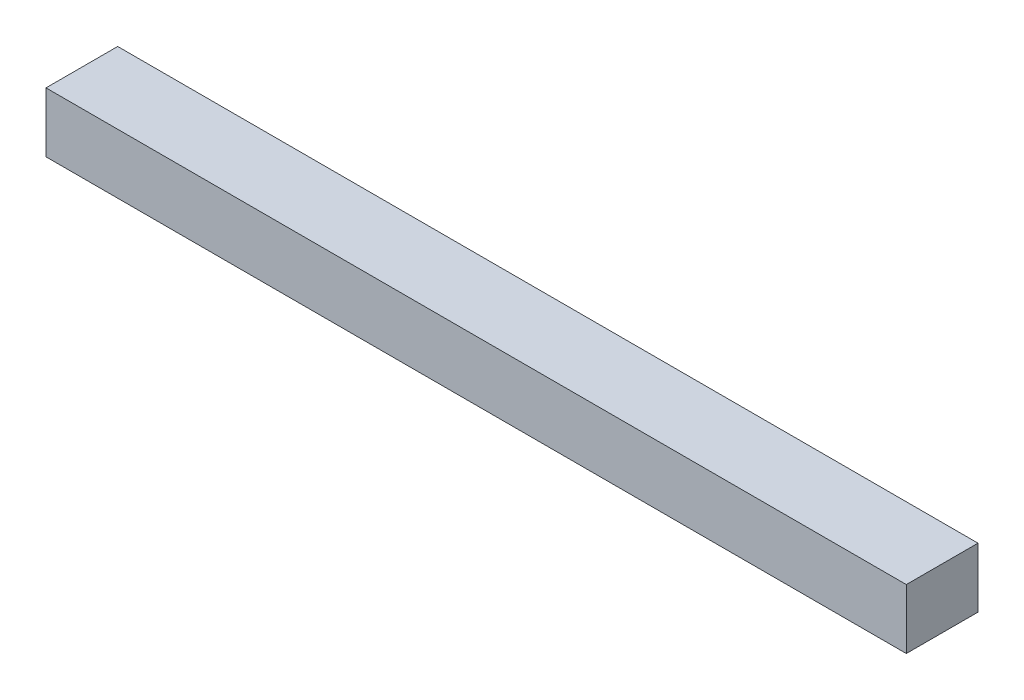
SolidWorks part; units mm, degrees
ref_plane "Спереди" through (0, 0, 0) normal (0, 0, 1) x (1, 0, 0)
ref_plane "Сверху" through (0, 0, 0) normal (0, 1, 0) x (1, 0, 0)
ref_plane "Справа" through (0, 0, 0) normal (1, 0, 0) x (0, 0, -1)
sketch "Эскиз2" plane through (0, 0, 0) normal (1, 0, 0) x (0, 0, -1)
  line L1 (-15, -12.5) -> (15, -12.5)
  line L2 (-15, -12.5) -> (-15, 12.5)
  line L3 (-15, 12.5) -> (15, 12.5)
  line L4 (15, -12.5) -> (15, 12.5)
  line L5 (-15, -12.5) -> (15, 12.5) construction
  line L6 (-15, 12.5) -> (15, -12.5) construction
  point P0 (0, 0)
extrude "Бобышка-Вытянуть1" add sketch "Эскиз2" along normal blind 360
